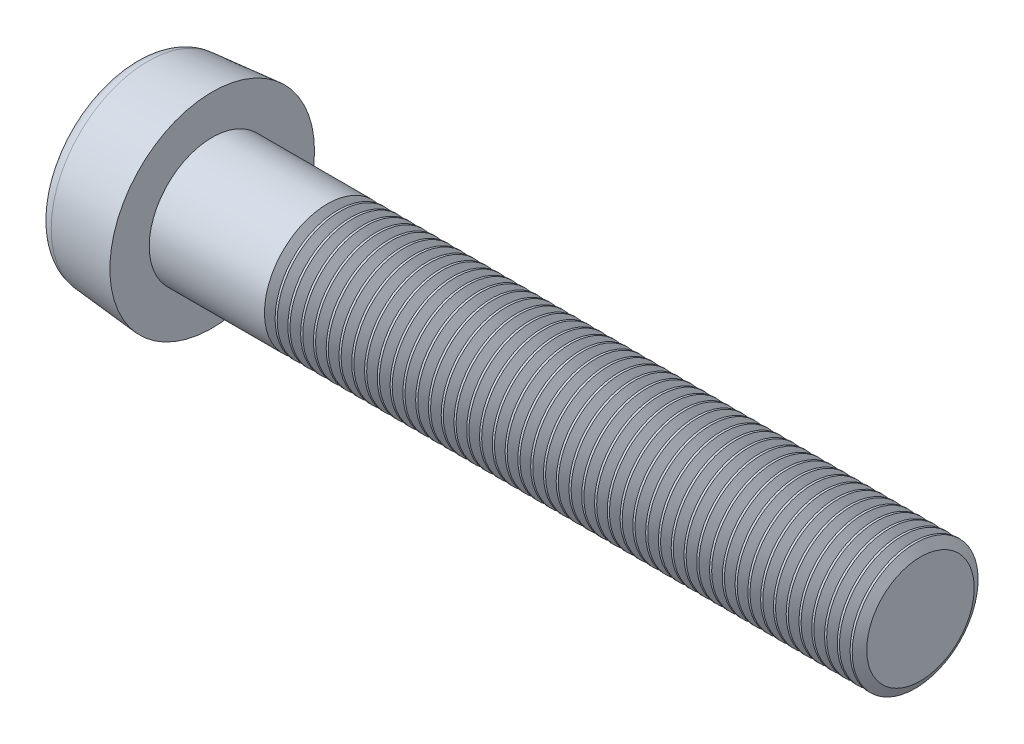
SolidWorks part; units mm, degrees
ref_plane "Front" through (0, 0, 0) normal (0, 0, 1) x (1, 0, 0)
ref_plane "Top" through (0, 0, 0) normal (0, 1, 0) x (1, 0, 0)
ref_plane "Right" through (0, 0, 0) normal (1, 0, 0) x (0, 0, -1)
ref_plane "Plane1" through (5, 0, 0) normal (1, 0, 0) x (0, 0, -1)
sketch "Sketch1" plane through (5, 0, 0) normal (1, 0, 0) x (0, 0, -1)
  circle A0 centre (0, 0) radius 6.5
  dimension "dk" = 13
extrude "BaseHead" add sketch "Sketch1" against normal blind 5 draft 5
sketch "Sketch2" plane through (5, 0, 0) normal (1, 0, 0) x (0, 0, -1)
  circle A0 centre (0, 0) radius 3
  dimension "d" = 6
sketch "Sketch8" plane through (0, 0, 0) normal (0, 0, 1) x (1, 0, 0)
  line L0 (0, 0) -> (35.73, 0) construction
  line L1 (7.1525, 0) -> (7.1525, -2) construction
  line L2 (5, -6.5) -> (5, 6.5) construction
  line L3 (11.6578, 0) -> (11.6578, -7.188) construction
  line L4 (5, 4) -> (50, 4)
  line L5 (50, 4) -> (50, 0)
  line L7 (50, 0) -> (5, 0)
  line L9 (5, 4) -> (5, 0)
  arc A0 (6.7996, -0.1884) -> (7.126, -0.3991) centre (7.1525, 0) ccw construction
  dimension "r" = 0.4
  dimension "d" = 8
  dimension "a" = 2
  dimension "l" = 45
  dimension "D4" = 7.188
revolve "Revolve1" add sketch "Sketch8" angle 360 about L0
cosmetic thread "ThreadCosmetic1" [suppressed] parameters "bb"=38, "THD_MINOR"=6.647
sketch "Sketch4" plane through (0, 0, 0) normal (1, 0, 0) x (0, 0, -1)
  line L1 (0, 2.8868) -> (-2.5, 1.4434) construction
  line L2 (-2.5, 1.4434) -> (-2.5, -1.4434) construction
  line L3 (-2.5, -1.4434) -> (0, -2.8868) construction
  line L4 (0, -2.8868) -> (2.5, -1.4434) construction
  line L5 (2.5, -1.4434) -> (2.5, 1.4434) construction
  line L6 (2.5, 1.4434) -> (0, 2.8868) construction
  line L7 (1.25, 2.1651) -> (-1.25, 2.1651) construction
  line L8 (-1.25, 2.1651) -> (-2.5, 0) construction
  line L9 (-2.5, 0) -> (-1.25, -2.1651) construction
  line L10 (-1.25, -2.1651) -> (1.25, -2.1651) construction
  line L11 (1.25, -2.1651) -> (2.5, 0) construction
  line L12 (2.5, 0) -> (1.25, 2.1651) construction
  circle A0 centre (0, 0) radius 2.8868 construction
  circle A1 centre (0, 0) radius 2.5 construction
  spline S0 degree 3 poles (0, 3.3309) (1.1538, 1.9985) (2.8846, 1.6654) (2.3077, 0) (2.8846, -1.6654) (1.1538, -1.9985) (0, -3.3309) (-1.1538, -1.9985) (-2.8846, -1.6654) (-2.3077, 0) (-2.8846, 1.6654) (-1.1538, 1.9985) (0, 3.3309) (1.1538, 1.9985) (2.8846, 1.6654) knots -0.25 -0.166667 -0.083333 0 0.083333 0.166667 0.25 0.333333 0.416667 0.5 0.583333 0.666667 0.75 0.833333 0.916667 1 1.083333 1.166667 1.25 only from (1.25, 2.1651) to (1.25, 2.1651)
  dimension "B" = 5
extrude "Socket" cut sketch "Sketch4" along normal blind 2.6
sketch "Sketch5" plane through (2.6, 0, 0) normal (-1, 0, 0) x (0, 0, 1)
  spline S1 degree 3 poles (0, 3.3309) (-1.1538, 1.9985) (-2.8846, 1.6654) (-2.3077, 0) (-2.8846, -1.6654) (-1.1538, -1.9985) (0, -3.3309) (1.1538, -1.9985) (2.8846, -1.6654) (2.3077, 0) (2.8846, 1.6654) (1.1538, 1.9985) (0, 3.3309) (-1.1538, 1.9985) (-2.8846, 1.6654) knots -0.25 -0.166667 -0.083333 0 0.083333 0.166667 0.25 0.333333 0.416667 0.5 0.583333 0.666667 0.75 0.833333 0.916667 1 1.083333 1.166667 1.25 only from (-1.25, 2.1651) to (-1.25, 2.1651)
  spline S2 degree 3 poles (0, 3.3309) (-1.1538, 1.9985) (-2.8846, 1.6654) (-2.3077, 0) (-2.8846, -1.6654) (-1.1538, -1.9985) (0, -3.3309) (1.1538, -1.9985) (2.8846, -1.6654) (2.3077, 0) (2.8846, 1.6654) (1.1538, 1.9985) (0, 3.3309) (-1.1538, 1.9985) (-2.8846, 1.6654) knots -0.25 -0.166667 -0.083333 0 0.083333 0.166667 0.25 0.333333 0.416667 0.5 0.583333 0.666667 0.75 0.833333 0.916667 1 1.083333 1.166667 1.25 only from (-1.25, 2.1651) to (-1.25, 2.1651)
  dimension "D1" = 0
ref_plane "Plane2" through (3.4667, 0, 0) normal (-1, 0, 0) x (0, 0, 1)
sketch "Sketch7" plane through (3.4667, 0, 0) normal (-1, 0, 0) x (0, 0, 1)
  point P0 (0, 0)
loft "Cut-Loft1" cut profiles "Sketch7", "Sketch5"
sketch "Sketch6" plane through (-30.7487, 13.2487, 0) normal (0, 0, 1) x (0, -1, 0)
  line L0 (13.2487, 89.8637) -> (13.2487, 24.8312) construction
  line L1 (-5.0748, 35.7487) -> (9.8252, 35.7487)
  line L2 (-5.0748, 35.7487) -> (-5.0748, 42.7487)
  line L3 (-5.0748, 42.7487) -> (9.2487, 42.7487)
  line L4 (9.9252, 35.8487) -> (9.9252, 39.5487)
  line L5 (17.2487, 80.7487) -> (9.2487, 80.7487) construction
  line L6 (9.2487, 42.7487) -> (9.9252, 39.5487)
  line L9 (19.7487, 35.7487) -> (6.7487, 35.7487) construction
  arc A0 (9.8252, 35.7487) -> (9.9252, 35.8487) centre (9.8252, 35.8487) ccw
  dimension "r" = 0.1
  dimension "d1" = 6.647
  dimension "D2" = 15
  dimension "x" = 3.2
  dimension "b" = 38
  dimension "D3" = 8
fillet "HeadFillet2" radius 1 1 edges at (0, 0, -6.0626)
sketch "Sketch9" plane through (0, 0, 0) normal (0, 0, 1) x (1, 0, 0)
  line L0 (50, 3.4141) -> (50.3382, 4)
  line L1 (50.3382, 4) -> (50.3382, 4.6765)
  line L2 (50.3382, 4.6765) -> (49.6617, 4.6765)
  line L3 (49.6617, 4.6765) -> (49.6617, 4)
  line L4 (49.6617, 4) -> (50, 3.4141)
  line L5 (50, -4) -> (50, 4) construction
  line L6 (0, 0) -> (28.2938, 0) construction
  line L7 (0, 5.1462) -> (0, -5.1462) construction
  dimension "D1" = 0.6765
  dimension "D2" = 8
revolve "Cut-Revolve10" cut sketch "Sketch9" angle 360 about L6
pattern_linear "LPattern10" count 47 spacing 0.8118 along (-1, 0, 0) of "Cut-Revolve10"
equation "\"D1@Plane1\"=\"k@BaseHead\""
equation "\"D1@Plane2\" = \"t@Socket\" / 3"
equation "\"D2@Sketch9\" =\"d@Sketch8\""
equation "\"D1@Sketch9\" =  ( \"d@Sketch8\" - \"THD_MINOR@ThreadCosmetic1\" )  / 2"
equation "\"D3@LPattern10\" = \"D1@Sketch9\" * 1.2"
equation "\"D1@LPattern10\" = \"bb@ThreadCosmetic1\" / \"D3@LPattern10\" "
equation "\"D3@Sketch6\" = \"d@Sketch8\""
